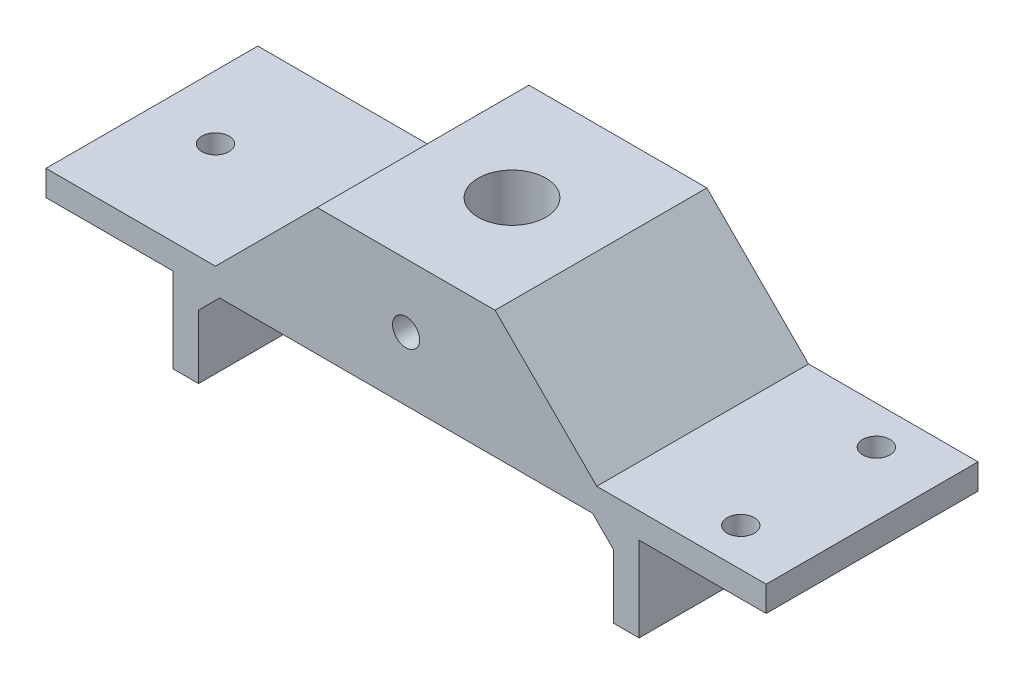
SolidWorks part; units mm, degrees
material "6061 合金"
ref_plane "前视基准面" through (0, 0, 0) normal (0, 0, 1) x (1, 0, 0)
ref_plane "上视基准面" through (0, 0, 0) normal (0, 1, 0) x (1, 0, 0)
ref_plane "右视基准面" through (0, 0, 0) normal (1, 0, 0) x (0, 0, -1)
sketch "草图1" plane through (0, 0, 0) normal (0, 0, 1) x (1, 0, 0)
  line L0 (-42.5, 0) -> (42.5, 0)
  dimension "D1" = 85
extrude "拉伸-薄壁1" add sketch "草图1" along normal blind 25 thin
sketch "草图2" plane through (0, -3, 0) normal (0, -1, 0) x (1, 0, 0)
  line L0 (-27.5, 0) -> (-27.5, 25)
  line L1 (-42.5, 0) -> (42.5, 0) construction
  line L2 (-42.5, 25) -> (42.5, 25) construction
  line L3 (-42.5, 25) -> (-42.5, 0) construction
  dimension "D1" = 15
extrude "拉伸-薄壁2" add sketch "草图2" along normal blind 10 thin
sketch "草图3" plane through (0, -3, 0) normal (0, -1, 0) x (1, 0, 0)
  line L0 (27.5, 25) -> (27.5, 0)
  line L1 (-24.5, 25) -> (42.5, 25) construction
  line L2 (-24.5, 0) -> (42.5, 0) construction
  line L3 (42.5, 25) -> (42.5, 0) construction
  dimension "D1" = 15
extrude "拉伸-薄壁3" add sketch "草图3" along normal blind 10 thin
sketch "草图4" plane through (0, 0, 0) normal (0, 1, 0) x (1, 0, 0)
  line L0 (0, 0) -> (0, -25) construction
  line L1 (-42.5, -25) -> (42.5, -25) construction
  line L2 (-42.5, 0) -> (42.5, 0) construction
  line L3 (-12.5, -25) -> (12.5, -25)
  line L4 (-12.5, -25) -> (-12.5, 0)
  line L5 (-12.5, 0) -> (12.5, 0)
  line L6 (12.5, -25) -> (12.5, 0)
  line L7 (-12.5, -25) -> (12.5, 0) construction
  line L8 (-12.5, 0) -> (12.5, -25) construction
  point P5 (0, -12.5)
  dimension "D1" = 25
extrude "凸台-拉伸1" add sketch "草图4" along normal blind 12
sketch "草图5" plane through (0, 12, 0) normal (0, 1, 0) x (1, 0, 0)
  line L0 (0, 0) -> (0, -25) construction
  line L1 (12.5, 0) -> (-12.5, 0) construction
  line L2 (-12.5, -25) -> (12.5, -25) construction
  circle A0 centre (0, -12.5) radius 4
  dimension "D1" = 8
extrude "切除-拉伸1" cut sketch "草图5" against normal up to next
sketch "草图6" plane through (0, 0, 25) normal (0, 0, 1) x (1, 0, 0)
  line L0 (0, 12) -> (0, -3) construction
  line L1 (-12.5, 12) -> (12.5, 12) construction
  line L2 (-24.5, -3) -> (24.5, -3) construction
  circle A0 centre (0, 4.5) radius 1.6
  dimension "D1" = 3.2
chamfer "倒角1" distance 10 angle 45 1 edges
chamfer "倒角2" distance 10 angle 45 1 edges
sketch "草图7" plane through (0, 0, 0) normal (0, 0, -1) x (-1, 0, 0)
  line L0 (-12.5, 10) -> (-10.5, 12)
  line L1 (-12.5, 12) -> (12.5, 12) construction
  line L2 (-10.5, 12) -> (-12.5, 12)
  line L3 (-12.5, 12) -> (-12.5, 10)
  line L4 (12.5, 10) -> (10.5, 12)
  line L5 (10.5, 12) -> (12.5, 12)
  line L6 (12.5, 12) -> (12.5, 10)
extrude "切除-拉伸3" cut sketch "草图7" against normal up to next
sketch "草图8" plane through (0, -3, 0) normal (0, -1, 0) x (1, 0, 0)
  line L0 (42.5, 12.5) -> (27.5, 12.5) construction
  line L1 (42.5, 25) -> (42.5, 0) construction
  line L2 (27.5, 25) -> (27.5, 0) construction
  line L3 (35, 12.5) -> (35, 4.5) construction
  line L4 (-27.5, 12.5) -> (-42.5, 12.5) construction
  line L5 (-27.5, 0) -> (-27.5, 25) construction
  line L6 (-42.5, 25) -> (-42.5, 0) construction
  circle A0 centre (35, 4.5) radius 1.6
  circle A1 centre (35, 20.5) radius 1.6
  circle A2 centre (-35, 12.5) radius 1.6
  dimension "D2" = 3.2
  dimension "D3" = 3.2
  dimension "D1" = 8
extrude "切除-拉伸4" cut sketch "草图8" against normal up to next
chamfer "倒角4" distance 2.5 angle 45 1 edges at (24.5, -3, 12.5)
chamfer "倒角5" distance 2.5 angle 45 1 edges
sketch "草图9" plane through (0, 0, 25) normal (0, 0, 1) x (1, 0, 0)
  line L0 (0, 12) -> (0, -3) construction
  line L1 (-10.5, 12) -> (10.5, 12) construction
  line L2 (-22, -3) -> (22, -3) construction
  circle A0 centre (0, 4.5) radius 1.6
  dimension "D1" = 3.2
extrude "切除-拉伸5" cut sketch "草图9" against normal up to surface (25 mm away) up to face at (-3.1667, -3.6528, 0)
